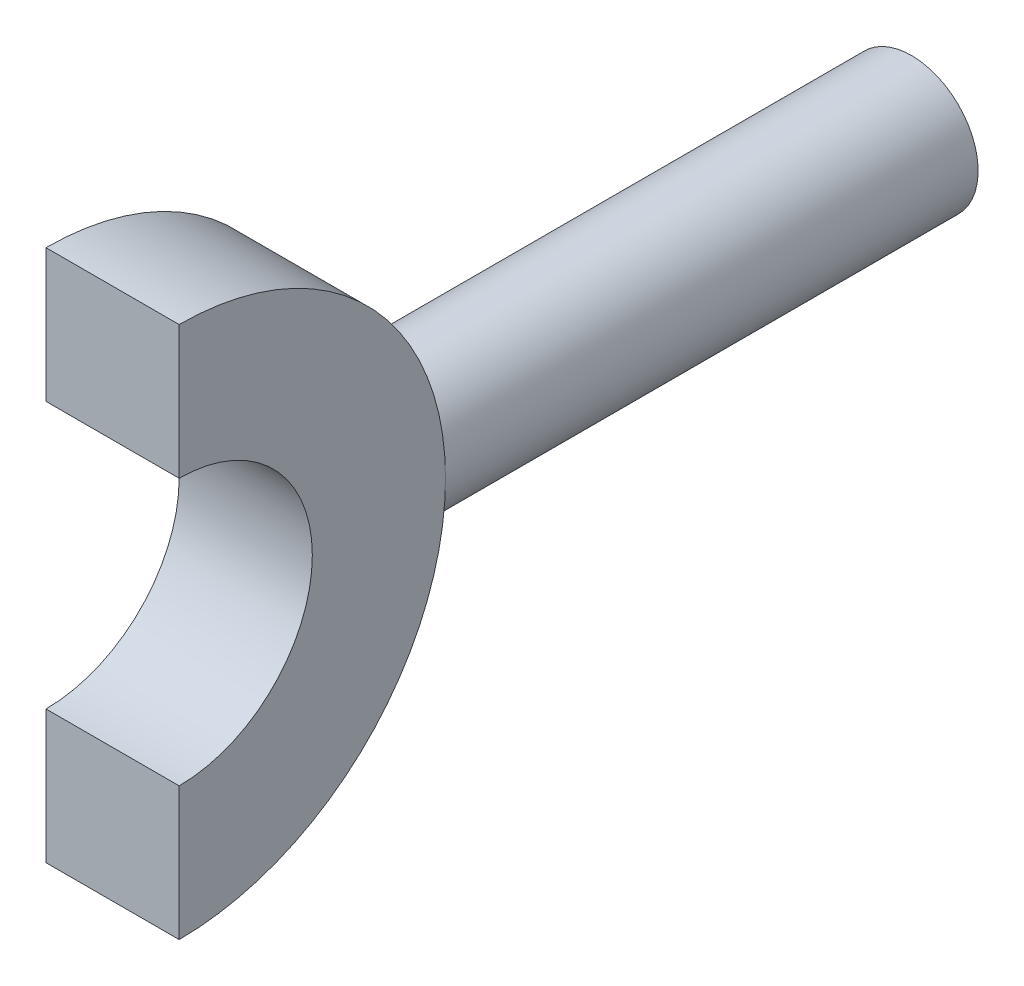
SolidWorks part; units mm, degrees
ref_plane "Front Plane" through (0, 0, 0) normal (0, 0, 1) x (1, 0, 0)
ref_plane "Top Plane" through (0, 0, 0) normal (0, 1, 0) x (1, 0, 0)
ref_plane "Right Plane" through (0, 0, 0) normal (1, 0, 0) x (0, 0, -1)
sketch "Sketch2" plane through (0, 0, 0) normal (1, 0, 0) x (0, 0, -1)
  circle A0 centre (0, 0) radius 10
  dimension "D1" = 20
extrude "Boss-Extrude1" add sketch "Sketch2" along normal mid plane 5
sketch "Sketch3" plane through (2.5, 0, 0) normal (1, 0, 0) x (0, 0, -1)
  line L0 (0, 5) -> (0, 10)
  line L1 (0, -5) -> (0, -10)
  arc A0 (0, -5) -> (0, 5) centre (0, 0) ccw
  circle A1 centre (0, 0) radius 10 construction
  arc A2 (0, 10) -> (0, -10) centre (0, 0) ccw
  dimension "D1" = 10
extrude "Cut-Extrude1" cut sketch "Sketch3" against normal through all both and the other way through all
ref_plane "Plane1" through (0, 0, -30) normal (0, 0, -1) x (-1, 0, 0)
sketch "Sketch4" plane through (0, 0, -30) normal (0, 0, -1) x (-1, 0, 0)
  line L0 (2.5, -10) -> (-2.5, -10) construction
  line L1 (2.5, -10) -> (2.5, 10) construction
  circle A0 centre (0, 0) radius 2.5
  point P2 (0, 0)
  point P6 (0, -10)
extrude "Boss-Extrude2" add sketch "Sketch4" against normal up to next
